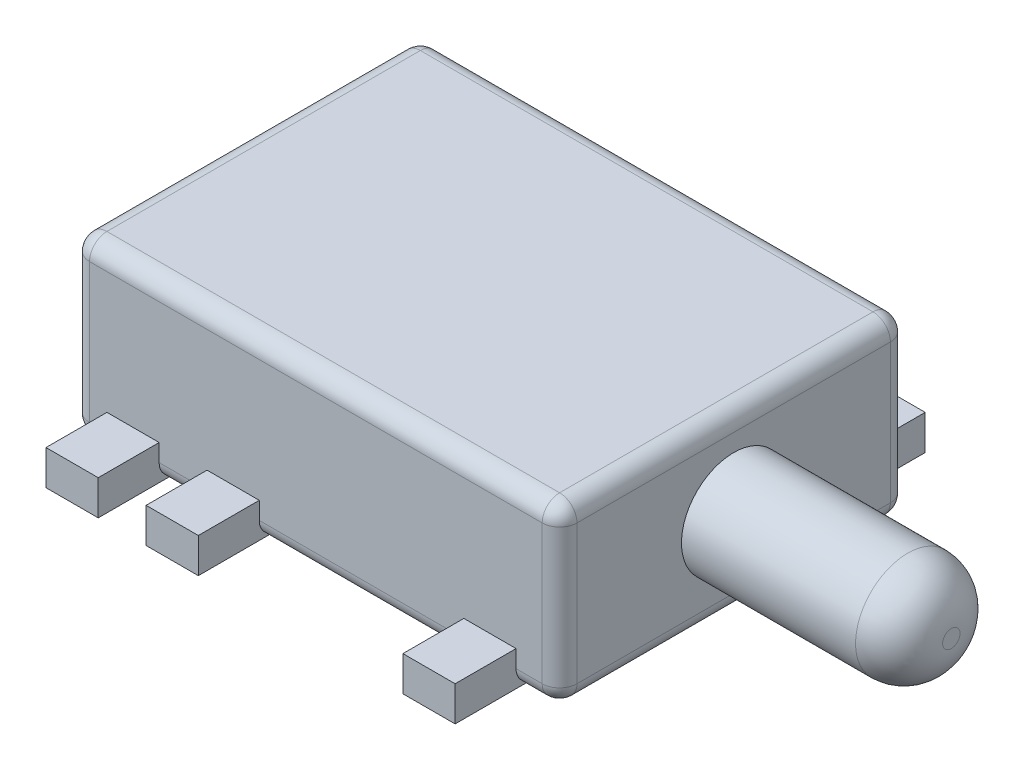
SolidWorks part; units mm, degrees
material "1023 Листовая углеродистая сталь (SS)"
ref_plane "Спереди" through (0, 0, 0) normal (0, 0, 1) x (1, 0, 0)
ref_plane "Сверху" through (0, 0, 0) normal (0, 1, 0) x (1, 0, 0)
ref_plane "Справа" through (0, 0, 0) normal (1, 0, 0) x (0, 0, -1)
sketch "Эскиз1" plane through (0, 0, 0) normal (0, 1, 0) x (1, 0, 0)
  line L1 (-2.8, -2) -> (2.8, -2)
  line L2 (-2.8, -2) -> (-2.8, 2)
  line L3 (-2.8, 2) -> (2.8, 2)
  line L4 (2.8, -2) -> (2.8, 2)
  line L5 (-2.8, -2) -> (2.8, 2) construction
  line L6 (-2.8, 2) -> (2.8, -2) construction
  point P0 (0, 0)
  dimension "D1" = 5.6
  dimension "D2" = 4
extrude "Бобышка-Вытянуть1" add sketch "Эскиз1" along normal blind 2
sketch "Эскиз2" plane through (2.8, 0, 0) normal (1, 0, 0) x (0, 0, -1)
  line L0 (0, 0) -> (0, 1) construction
  line L1 (-2, 0) -> (2, 0) construction
  circle A0 centre (0, 1) radius 0.6
  dimension "D2" = 1.2
  dimension "D1" = 1
extrude "Бобышка-Вытянуть2" add sketch "Эскиз2" along normal blind 2.5
fillet "Скругление1" radius 0.5 1 edges at (5.3, 1, -0.6)
sketch "Эскиз3" plane through (0, 0, 0) normal (0, -1, 0) x (1, 0, 0)
  line L0 (2.8, 2) -> (2.8, -2) construction
  line L1 (-2.4, 2.7) -> (-1.8, 2.7)
  line L2 (-2.4, 2.7) -> (-2.4, -2.7)
  line L3 (-2.4, -2.7) -> (-1.8, -2.7)
  line L4 (-1.8, 2.7) -> (-1.8, -2.7)
  line L5 (-2.4, 2.7) -> (-1.8, -2.7) construction
  line L6 (-2.4, -2.7) -> (-1.8, 2.7) construction
  line L7 (-1.25, 2.7) -> (-0.65, 2.7)
  line L8 (-1.25, 2.7) -> (-1.25, -2.7)
  line L9 (-1.25, -2.7) -> (-0.65, -2.7)
  line L10 (-0.65, 2.7) -> (-0.65, -2.7)
  line L11 (-1.25, 2.7) -> (-0.65, -2.7) construction
  line L12 (-1.25, -2.7) -> (-0.65, 2.7) construction
  line L13 (1.7, 2.7) -> (2.3, 2.7)
  line L14 (1.7, 2.7) -> (1.7, -2.7)
  line L15 (1.7, -2.7) -> (2.3, -2.7)
  line L16 (2.3, 2.7) -> (2.3, -2.7)
  line L17 (1.7, 2.7) -> (2.3, -2.7) construction
  line L18 (1.7, -2.7) -> (2.3, 2.7) construction
  point P0 (-2.1, 0)
  point P5 (-0.95, 0)
  point P10 (2, 0)
  point P15 (0, 0)
  dimension "D1" = 0.6
  dimension "D2" = 4.9
  dimension "D3" = 3.75
  dimension "D4" = 5.4
  dimension "D5" = 0.8
extrude "Бобышка-Вытянуть3" add sketch "Эскиз3" against normal blind 0.4
sketch "Эскиз4" plane through (0, 0, 0) normal (0, -1, 0) x (1, 0, 0)
  line L0 (5.3, -0.1) -> (5.3, 0.1) construction
  circle A0 centre (-1.45, 0) radius 0.4
  circle A1 centre (1.55, 0) radius 0.4
  point P6 (0, 0)
  dimension "D3" = 0.8
  dimension "D1" = 3.75
  dimension "D2" = 3
extrude "Бобышка-Вытянуть4" add sketch "Эскиз4" along normal blind 0.6
chamfer "Фаска1" distance 0.1 angle 45 2 edges at (1.55, -0.6, -0.4) (-1.45, -0.6, -0.4)
fillet "Скругление2" radius 0.2 18 edges at (0, 2, 2) (-2.8, 2, 0) (0, 2, -2) (2.8, 2, 0) (2.8, 1, -2) (2.55, 0, -2) (0.525, 0, -2) (-1.525, 0, -2) (-2.6, 0, -2) (-2.8, 1, -2) (-2.8, 0, 0) (-2.6, 0, 2) (-2.8, 1, 2) (-1.525, 0, 2) (2.8, 1, 2) (2.55, 0, 2) (0.525, 0, 2) (2.8, 0, 0)
